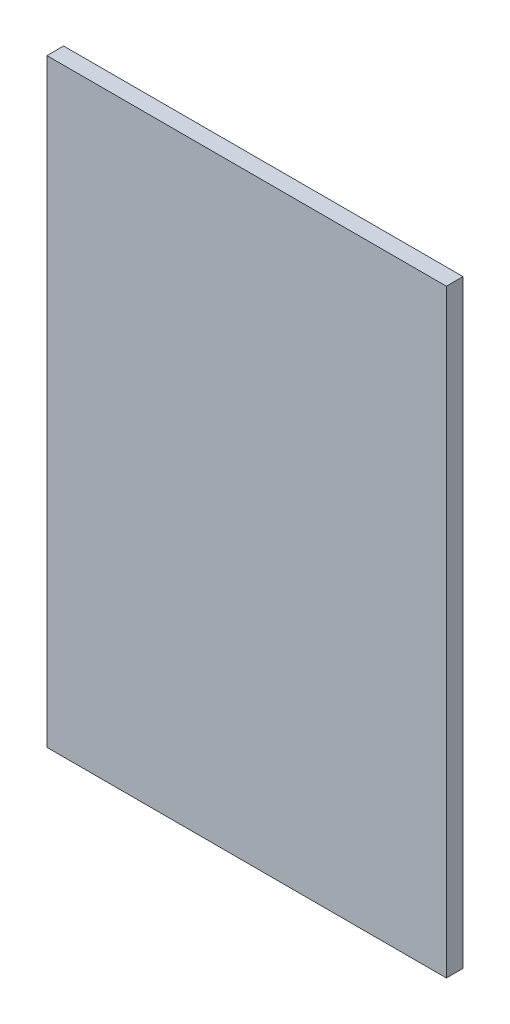
SolidWorks part; units mm, degrees
ref_plane "Front Plane" through (0, 0, 0) normal (0, 0, 1) x (1, 0, 0)
ref_plane "Top Plane" through (0, 0, 0) normal (0, 1, 0) x (1, 0, 0)
ref_plane "Right Plane" through (0, 0, 0) normal (1, 0, 0) x (0, 0, -1)
sketch "Sketch1" plane through (0, 0, 0) normal (0, 0, 1) x (1, 0, 0)
  line L1 (-60, -90) -> (60, -90)
  line L2 (-60, -90) -> (-60, 90)
  line L3 (-60, 90) -> (60, 90)
  line L4 (60, -90) -> (60, 90)
  line L5 (-60, -90) -> (60, 90) construction
  line L6 (-60, 90) -> (60, -90) construction
  point P0 (0, 0)
  dimension "D1" = 120
  dimension "D2" = 180
extrude "Boss-Extrude1" add sketch "Sketch1" along normal blind 5
sketch "Sketch2" plane through (0, 0, 0) normal (0, 0, -1) x (-1, 0, 0)
  line L10 (-60, 90) -> (60, 90) construction
  line L11 (-4, -70) -> (4, -70)
  line L12 (-4, -70) -> (-4, 70)
  line L13 (-4, 70) -> (4, 70)
  line L14 (4, -70) -> (4, 70)
  line L15 (-4, -70) -> (4, 70) construction
  line L16 (-4, 70) -> (4, -70) construction
  point P0 (0, 0)
  dimension "D1" = 8
  dimension "D2" = 20
extrude "Boss-Extrude2" add sketch "Sketch2" along normal blind 14
